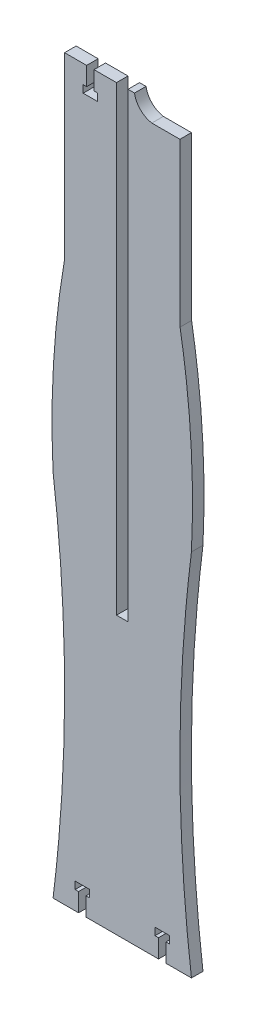
SolidWorks part; units mm, degrees
ref_plane "Front Plane" through (0, 0, 0) normal (0, 0, 1) x (1, 0, 0)
ref_plane "Top Plane" through (0, 0, 0) normal (0, 1, 0) x (1, 0, 0)
ref_plane "Right Plane" through (0, 0, 0) normal (1, 0, 0) x (0, 0, -1)
sketch "Sketch2" plane through (0, 0, 0) normal (0, 0, 1) x (1, 0, 0)
  line L0 (-6.35, 101.6) -> (48.849, 101.6) construction
  line L1 (-41.275, 0) -> (-27.2233, 0)
  line L2 (-35.0152, 307.2735) -> (-34.925, 406.4)
  line L3 (-34.925, 406.4) -> (-22.7965, 406.4)
  line L4 (0, 406.4) -> (3.5795, 406.4)
  line L5 (-3.175, 152.4) -> (-3.175, 101.6) construction
  line L6 (-6.35, 152.4) -> (-6.35, 406.4)
  line L7 (-6.35, 152.4) -> (0, 152.4)
  line L8 (0, 152.4) -> (0, 406.4)
  line L9 (28.5837, 396.8455) -> (28.6652, 307.2735)
  line L10 (-3.175, 0) -> (-3.175, 25.2362) construction
  line L11 (-25.1913, -3.5806) -> (-25.1913, 12.1691) construction
  line L12 (-27.2233, 0) -> (-27.2233, 10.16)
  line L13 (-27.2233, 10.16) -> (-29.1283, 10.16)
  line L14 (-29.1283, 10.16) -> (-29.1283, 14.224)
  line L15 (-29.1283, 14.224) -> (-21.2543, 14.224)
  line L16 (-23.1593, 0) -> (-23.1593, 10.16)
  line L17 (-23.1593, 10.16) -> (-21.2543, 10.16)
  line L18 (-21.2543, 10.16) -> (-21.2543, 14.224)
  line L19 (-23.1593, 0) -> (16.8093, 0)
  line L20 (16.8093, 0) -> (16.8093, 10.16)
  line L21 (16.8093, 10.16) -> (14.9043, 10.16)
  line L22 (14.9043, 10.16) -> (14.9043, 14.224)
  line L23 (22.7783, 14.224) -> (14.9043, 14.224)
  line L24 (22.7783, 10.16) -> (22.7783, 14.224)
  line L25 (20.8733, 10.16) -> (22.7783, 10.16)
  line L26 (20.8733, 0) -> (20.8733, 10.16)
  line L27 (20.8733, 0) -> (34.925, 0)
  line L28 (-20.7645, 406.4) -> (-20.7645, 413.7223) construction
  line L29 (28.5837, 396.8455) -> (13.1098, 396.8455)
  line L30 (-22.7965, 406.4) -> (-22.7965, 396.24)
  line L31 (-22.7965, 396.24) -> (-24.7015, 396.24)
  line L32 (-24.7015, 396.24) -> (-24.7015, 392.176)
  line L33 (-24.7015, 392.176) -> (-20.7645, 392.176)
  line L34 (-20.7645, 392.176) -> (-16.8275, 392.176)
  line L35 (-16.8275, 396.24) -> (-16.8275, 392.176)
  line L36 (-18.7325, 396.24) -> (-16.8275, 396.24)
  line L37 (-18.7325, 406.4) -> (-18.7325, 396.24)
  line L38 (-18.7325, 406.4) -> (-6.35, 406.4)
  arc A0 (3.5795, 406.4) -> (13.1098, 396.8455) centre (15.0244, 408.2856) ccw
  spline S0 degree 2 poles (-35.0152, 307.2735) (-43.8491, 256.2238) (-41.275, 203.2) knots 0.497444 0.497444 0.497444 1 1 1
  spline S1 degree 2 poles (28.6652, 307.2735) (37.4991, 256.2238) (34.925, 203.2) knots 0.497444 0.497444 0.497444 1 1 1
  spline S2 degree 2 poles (-41.275, 203.2) (-28.575, 101.6) (-41.275, 0) knots 0 0 0 1 1 1
  spline S3 degree 2 poles (34.925, 203.2) (22.225, 101.6) (34.925, 0) knots 0 0 0 1 1 1
  point P42 (-25.1913, 14.224)
  dimension "D1" = 76.2
  dimension "D2" = 31.75
  dimension "D3" = 31.75
  dimension "D4" = 2.032
  dimension "D5" = 4.064
  dimension "D6" = 3.937
  dimension "D7" = 14.224
  dimension "D8" = 14.224
  dimension "D9" = 2.032
  dimension "D10" = 3.937
  dimension "D11" = 4.064
  dimension "D12" = 1.905
extrude "Boss-Extrude1" add sketch "Sketch2" along normal blind 6.35
